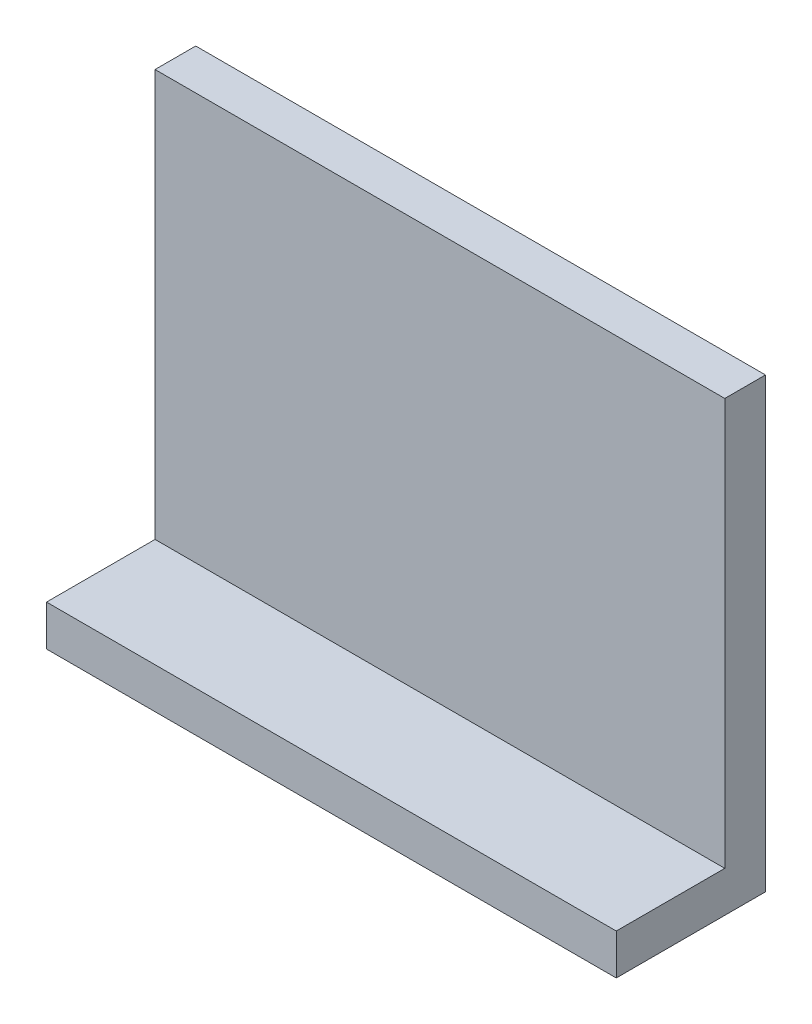
SolidWorks part; units mm, degrees
ref_plane "Front Plane" through (0, 0, 0) normal (0, 0, 1) x (1, 0, 0)
ref_plane "Top Plane" through (0, 0, 0) normal (0, 1, 0) x (1, 0, 0)
ref_plane "Right Plane" through (0, 0, 0) normal (1, 0, 0) x (0, 0, -1)
sketch "Sketch1" plane through (0, 0, 0) normal (0, 0, 1) x (1, 0, 0)
  line L1 (0, 0) -> (42, 0)
  line L2 (0, 0) -> (0, 33)
  line L3 (0, 33) -> (42, 33)
  line L4 (42, 0) -> (42, 33)
extrude "Boss-Extrude1" add sketch "Sketch1" along normal blind 3
sketch "Sketch2" plane through (0, 0, 3) normal (0, 0, 1) x (1, 0, 0)
  line L0 (42, 0) -> (42, 33) construction
  line L1 (0, 0) -> (42, 0)
  line L2 (0, 0) -> (0, 3)
  line L3 (0, 3) -> (42, 3)
  line L4 (42, 0) -> (42, 3)
extrude "Boss-Extrude2" add sketch "Sketch2" along normal blind 8
